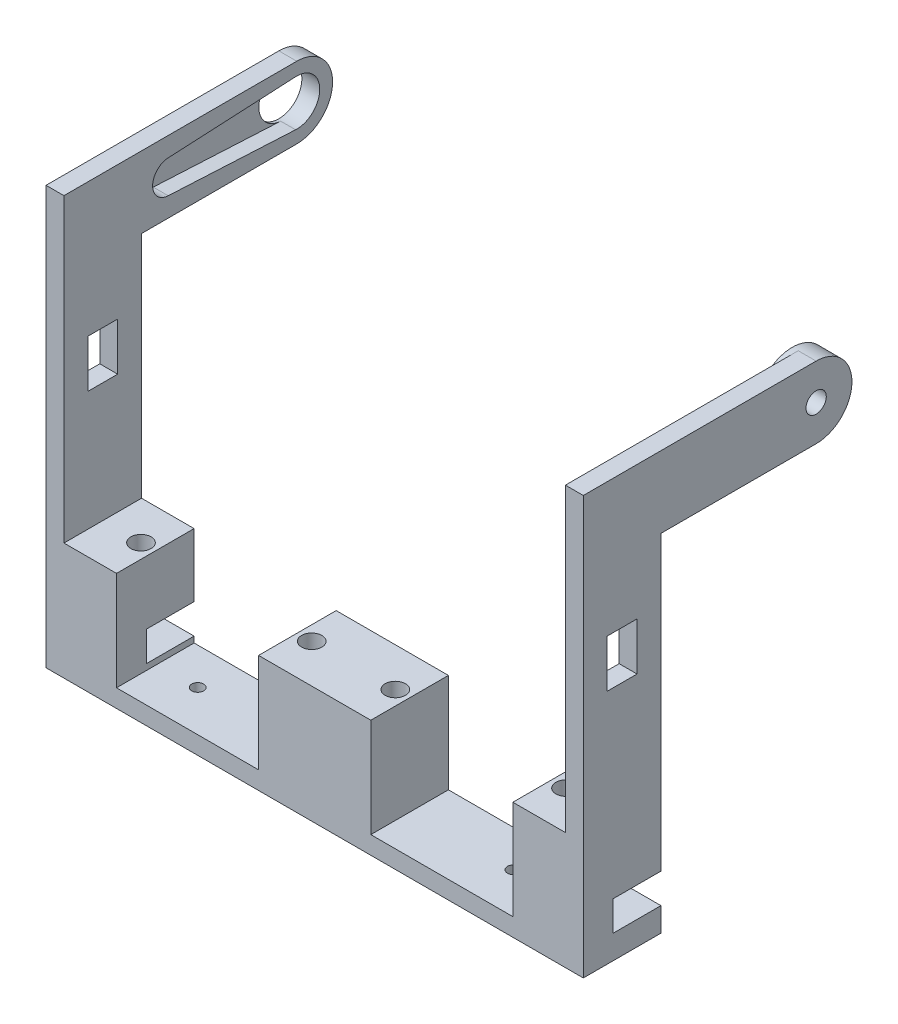
SolidWorks part; units mm, degrees
ref_plane "Ebene vorne" through (0, 0, 0) normal (0, 0, 1) x (1, 0, 0)
ref_plane "Ebene oben" through (0, 0, 0) normal (0, 1, 0) x (1, 0, 0)
ref_plane "Ebene rechts" through (0, 0, 0) normal (1, 0, 0) x (0, 0, -1)
sketch "Skizze1" plane through (0, 0, 0) normal (0, 0, 1) x (1, 0, 0)
  line L0 (-45, 67) -> (-42, 67)
  line L1 (-42, 67) -> (-42, 0)
  line L2 (-42, 0) -> (42, 0)
  line L3 (-45, 67) -> (-45, -3)
  line L4 (-45, -3) -> (45, -3)
  line L5 (0, -3) -> (0, 0) construction
  line L7 (45, 67) -> (45, -3)
  line L8 (42, 67) -> (42, 0)
  line L9 (45, 67) -> (42, 67)
  dimension "D1" = 90
  dimension "D2" = 3
  dimension "D3" = 70
  dimension "D4" = 3
extrude "Aufsatz-Linear austragen1" add sketch "Skizze1" along normal blind 13
sketch "Skizze2" plane through (0, 0, 0) normal (0, 0, -1) x (-1, 0, 0)
  line L0 (-42, 67) -> (-42, 0) construction
  line L1 (-45, 67) -> (-42, 67)
  line L2 (-45, 67) -> (-45, 55)
  line L3 (-45, 55) -> (-42, 55)
  line L4 (-42, 67) -> (-42, 55)
  line L5 (0, 55.836) -> (0, 0) construction
  line L6 (42, 67) -> (42, 55)
  line L7 (45, 55) -> (42, 55)
  line L8 (45, 67) -> (45, 55)
  line L9 (45, 67) -> (42, 67)
  dimension "D1" = 12
extrude "Aufsatz-Linear austragen2" add sketch "Skizze2" along normal blind 45 from surface at -13 starting at face at (0, 32.75, 13)
sketch "Skizze3" plane through (0, 0, 0) normal (0, 1, 0) x (1, 0, 0)
  line L0 (42, 0) -> (-42, 0) construction
  line L1 (-42, 0) -> (-33.2, 0)
  line L2 (-42, 0) -> (-42, -13)
  line L3 (-42, -13) -> (-33.2, -13)
  line L4 (-33.2, 0) -> (-33.2, -13)
  line L5 (42, -13) -> (-42, -13) construction
  line L6 (-42, -13) -> (-42, 32) construction
  line L7 (0, 0) -> (0, -13) construction
  line L8 (33.2, 0) -> (33.2, -13)
  line L9 (42, -13) -> (33.2, -13)
  line L10 (42, 0) -> (42, -13)
  line L11 (42, 0) -> (33.2, 0)
  line L12 (42, -13) -> (42, 0) construction
  line L13 (-32.7, -0.45) -> (-32.7, -12.55) construction
  line L14 (-9.9, -12.55) -> (-9.9, -0.45) construction
  line L15 (9.4, -13) -> (-9.4, -13)
  line L16 (9.4, -13) -> (9.4, 0)
  line L17 (9.4, 0) -> (-9.4, 0)
  line L18 (-9.4, -13) -> (-9.4, 0)
  line L19 (9.4, -13) -> (-9.4, 0) construction
  line L20 (9.4, 0) -> (-9.4, -13) construction
  point P21 (0, -6.5)
  dimension "D1" = 0.5
  dimension "D2" = 0.5
extrude "Aufsatz-Linear austragen3" add sketch "Skizze3" along normal up to surface (16.6 mm away)
sketch "Skizze4" plane through (0, 16.6, 0) normal (0, 1, 0) x (1, 0, 0)
  line L0 (-21.3, 1.2842) -> (-21.3, -15.8796) construction
  line L2 (0, -17.1221) -> (0, 0) construction
  circle A0 centre (-35.6, -6.5) radius 1.7
  circle A1 centre (-7, -6.5) radius 1.7
  circle A2 centre (7, -6.5) radius 1.7
  circle A3 centre (35.6, -6.5) radius 1.7
  dimension "D1" = 3.4
extrude "Schnitt-Linear austragen1" cut sketch "Skizze4" against normal blind 4
sketch "Skizze5" plane through (-45, 0, 0) normal (-1, 0, 0) x (0, 0, 1)
  line L0 (13, 67) -> (-32, 67) construction
  line L1 (-32, 67) -> (-32, 55) construction
  line L2 (-32, 55) -> (0, 55) construction
  circle A0 centre (-26, 61) radius 6
sketch "Skizze6" plane through (42, 0, 0) normal (-1, 0, 0) x (0, 0, 1)
  circle A0 centre (-26, 61) radius 1.5
  dimension "D1" = 3
extrude "Schnitt-Linear austragen2" cut sketch "Skizze6" against normal through all
sketch "Skizze7" plane through (-45, 0, 0) normal (-1, 0, 0) x (0, 0, 1)
  line L0 (-25.8021, 64.8449) -> (-4.4586, 63.7464)
  line L1 (-25.8021, 57.1551) -> (-4.4586, 58.2536)
  line L2 (-26, 61) -> (-4.6, 61) construction
  line L3 (-29.85, 67.01) -> (-29.85, 55.6644) construction
  line L5 (-1.85, 52.4429) -> (-1.85, 65.9427) construction
  arc A0 (-25.8021, 64.8449) -> (-25.8021, 57.1551) centre (-26, 61) ccw
  arc A1 (-4.4586, 63.7464) -> (-4.4586, 58.2536) centre (-4.6, 61) cw
  dimension "D1" = 3.85
  dimension "D2" = 2.75
  dimension "D3" = 28
extrude "Schnitt-Linear austragen4" cut sketch "Skizze7" along normal blind 2.5 from surface at -3 starting at face at (-42, 46.2, -6.3333)
sketch "Skizze10" plane through (-45, 0, 0) normal (-1, 0, 0) x (0, 0, 1)
  line L0 (13, 67) -> (-32, 67) construction
  line L1 (-32, 55) -> (0, 55) construction
  line L2 (-26, 55) -> (-40.1133, 55)
  line L3 (-40.1133, 55) -> (-40.1133, 67)
  line L4 (-40.1133, 67) -> (-26, 67)
  arc A0 (-26, 67) -> (-26, 55) centre (-26, 61) ccw
  circle A1 centre (-26, 61) radius 6 construction
  point P11 (-32, 61)
extrude "Schnitt-Linear austragen6" cut sketch "Skizze10" against normal through all
sketch "Skizze11" plane through (-44.5, 0, 0) normal (1, 0, 0) x (0, 0, -1)
  circle A1 centre (26, 61) radius 3.85
  arc A2 (25.8021, 64.8449) -> (25.8021, 57.1551) centre (26, 61) ccw construction
extrude "Schnitt-Linear austragen7" cut sketch "Skizze11" against normal up to next
sketch "Skizze12" plane through (45, 0, 0) normal (1, 0, 0) x (0, 0, -1)
  line L0 (0, -3) -> (0, 55) construction
  line L1 (0, 6) -> (-8, 6)
  line L2 (0, 6) -> (0, 1)
  line L3 (0, 1) -> (-8, 1)
  line L4 (-8, 6) -> (-8, 1)
  line L5 (0, 0) -> (-13, 0) construction
  dimension "D1" = 5
  dimension "D2" = 1
  dimension "D3" = 8
extrude "Schnitt-Linear austragen8" cut sketch "Skizze12" against normal blind 15 and the other way through all
ref_plane "Ebene1" through (0, 0, 0) normal (-1, 0, 0) x (0, 0, 1)
mirror "Spiegeln1" about plane through (0, 0, 0) normal (-1, 0, 0) of "Schnitt-Linear austragen8"
sketch "Skizze13" plane through (-45, 0, 0) normal (-1, 0, 0) x (0, 0, 1)
  line L5 (6.5, -3) -> (6.5, 40.6) construction
  line L6 (4, 44.6) -> (9, 44.6)
  line L7 (4, 44.6) -> (4, 36.6)
  line L8 (4, 36.6) -> (9, 36.6)
  line L9 (9, 44.6) -> (9, 36.6)
  line L10 (4, 44.6) -> (9, 36.6) construction
  line L11 (4, 36.6) -> (9, 44.6) construction
  line L12 (13, -3) -> (0, -3) construction
  line L13 (0, 16.6) -> (13, 16.6) construction
  point P0 (6.5, 40.6)
  dimension "D1" = 5
  dimension "D2" = 8
  dimension "D3" = 20
extrude "Schnitt-Linear austragen9" cut sketch "Skizze13" against normal through all
sketch "Skizze14" plane through (0, -3, 0) normal (0, -1, 0) x (-1, 0, 0)
  line L0 (0, 11.8421) -> (0, 0) construction
  line L1 (0, -7.15) -> (0, 7.15) construction
  circle A0 centre (26.45, -6.15) radius 1
  circle A1 centre (-26.45, -6.15) radius 1
  point P9 (0, 0)
  dimension "D1" = 2
extrude "Schnitt-Linear austragen10" cut sketch "Skizze14" against normal through all
sketch "Skizze15" plane through (42, 0, 0) normal (-1, 0, 0) x (0, 0, 1)
  circle A0 centre (-26, 61) radius 6
extrude "Aufsatz-Linear austragen4" add sketch "Skizze15" along normal blind 4 from surface at -3 starting at face at (45, 40.6, 6.5)
sketch "Skizze16" plane through (45, 0, 0) normal (1, 0, 0) x (0, 0, -1)
  circle A0 centre (26, 61) radius 1.7
  dimension "D1" = 3.4
extrude "Schnitt-Linear austragen11" cut sketch "Skizze16" against normal blind 3
equation "\"M2EinschmelzGewindeDurchmesser\"=3.4"
equation "\"M2EinschmelzGewindeTiefe\"= 4.0"
equation "\"M3EinschmelzGewindeDurchmesser\"= 4.2"
equation "\"M3EinschmelzGewindeTief\"= 5.7"
equation "\"M2SchraubeLoch\"=2.3"
equation "\"M3SchraubeLoch\"=3.3"
equation "\"offSetVonGummiReifen\"= 3.0"
equation "\"D1@Skizze4\"=\"M2EinschmelzGewindeDurchmesser\""
equation "\"D1@Schnitt-Linear austragen1\"=\"M2EinschmelzGewindeTiefe\""
equation "\"D1@Skizze16\"=\"M2EinschmelzGewindeDurchmesser\""
equation "\"D1@Schnitt-Linear austragen11\"=\"M2EinschmelzGewindeTiefe\""
